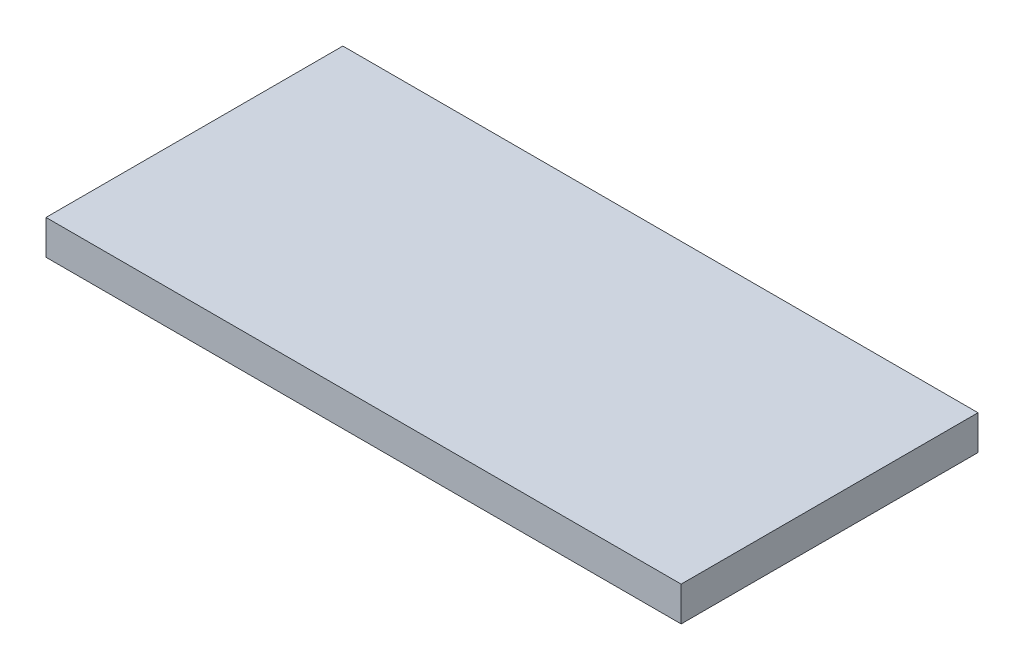
SolidWorks part; units mm, degrees
ref_plane "Front Plane" through (0, 0, 0) normal (0, 0, 1) x (1, 0, 0)
ref_plane "Top Plane" through (0, 0, 0) normal (0, 1, 0) x (1, 0, 0)
ref_plane "Right Plane" through (0, 0, 0) normal (1, 0, 0) x (0, 0, -1)
sketch "Sketch1" plane through (0, 0, 0) normal (0, 1, 0) x (1, 0, 0)
  line L1 (92, 43) -> (-92, 43)
  line L2 (92, 43) -> (92, -43)
  line L3 (92, -43) -> (-92, -43)
  line L4 (-92, 43) -> (-92, -43)
  line L5 (92, 43) -> (-92, -43) construction
  line L6 (92, -43) -> (-92, 43) construction
  point P0 (0, 0)
  dimension "D1" = 184
  dimension "D2" = 86
extrude "base" add sketch "Sketch1" along normal blind 10 contours L1 L4 L3 L2
sketch "Sketch2" plane through (0, 0, 0) normal (0, -1, 0) x (1, 0, 0)
  circle A0 centre (0, 0) radius 5.8
  dimension "D1" = 11.6
extrude "load cell button cut" cut sketch "Sketch2" against normal blind 5.2
equation "\"D2@Sketch1\"=46+40"
equation "\"D1@Sketch1\"=144+40"
